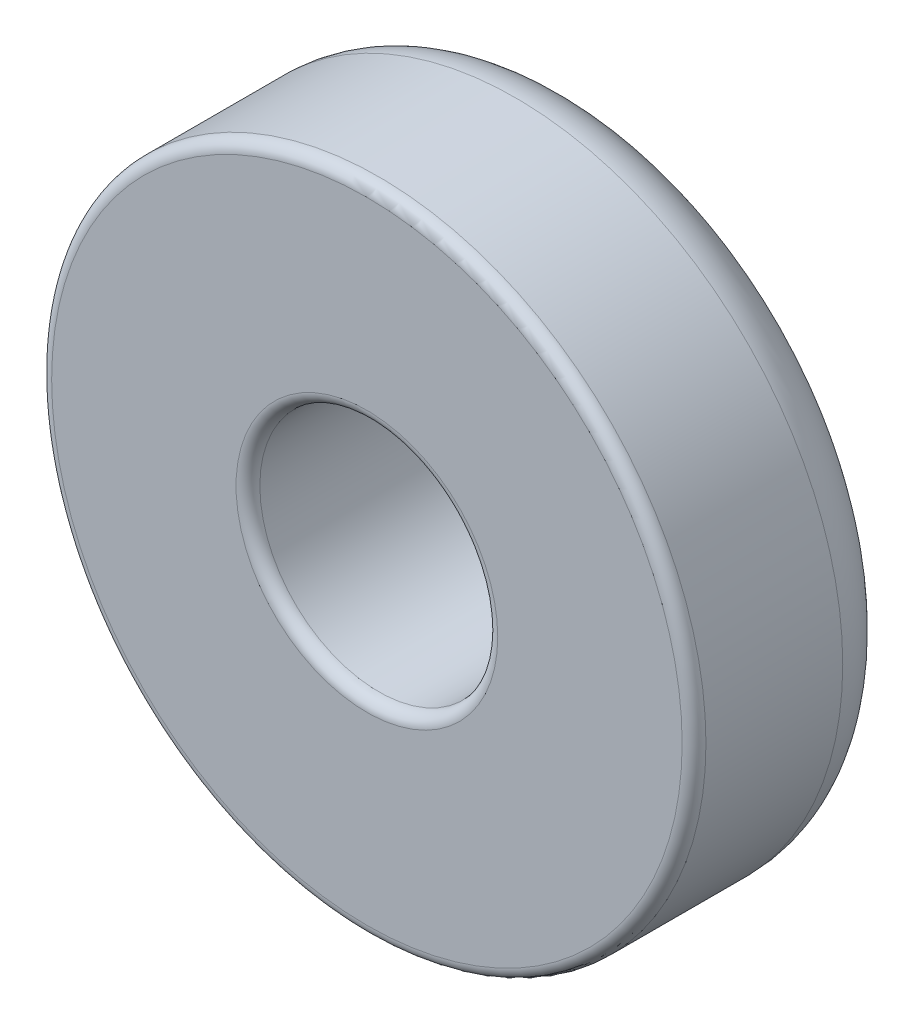
SolidWorks part; units mm, degrees
ref_plane "Front Plane" through (0, 0, 0) normal (0, 0, 1) x (1, 0, 0)
ref_plane "Top Plane" through (0, 0, 0) normal (0, 1, 0) x (1, 0, 0)
ref_plane "Right Plane" through (0, 0, 0) normal (1, 0, 0) x (0, 0, -1)
sketch "Sketch1" plane through (0, 0, 0) normal (0, 0, 1) x (1, 0, 0)
  circle A0 centre (0, 0) radius 1
  dimension "D1" = 2
extrude "Extrude-Thin1" add sketch "Sketch1" along normal blind 1.75 thin
fillet "Fillet1" radius 0.5 1 edges at (2.75, 0, 0)
fillet "Fillet2" radius 0.1 3 edges at (1, 0, 0) (1, 0, 1.75) (2.75, 0, 1.75)
scale "Scale1" scale about centroid uniform scaling yes scale factor 10
